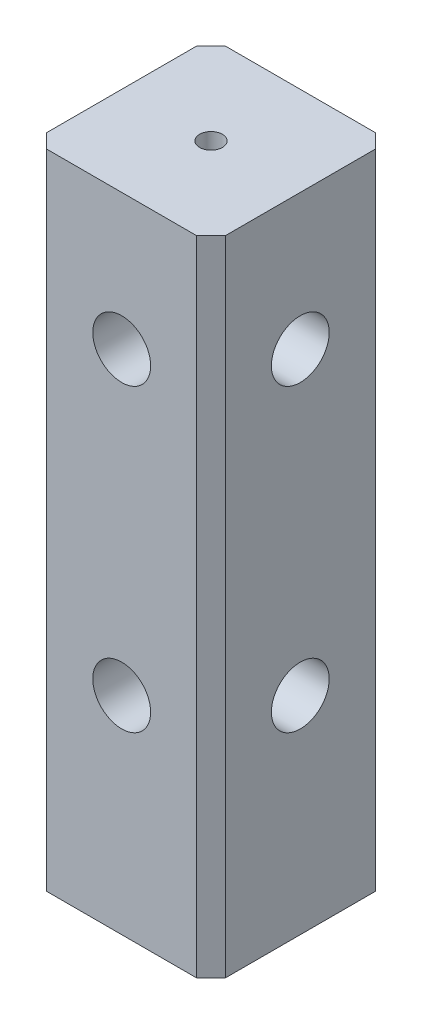
SolidWorks part; units mm, degrees
ref_plane "Front Plane" through (0, 0, 0) normal (0, 0, 1) x (1, 0, 0)
ref_plane "Top Plane" through (0, 0, 0) normal (0, 1, 0) x (1, 0, 0)
ref_plane "Right Plane" through (0, 0, 0) normal (1, 0, 0) x (0, 0, -1)
sketch "Sketch1" plane through (0, 0, 0) normal (0, 1, 0) x (1, 0, 0)
  line L1 (12.5, 12.5) -> (-12.5, 12.5)
  line L2 (12.5, 12.5) -> (12.5, -12.5)
  line L3 (12.5, -12.5) -> (-12.5, -12.5)
  line L4 (-12.5, 12.5) -> (-12.5, -12.5)
  point P4 (0, 12.5)
  point P6 (12.5, 0)
  dimension "D1" = 25
  dimension "D2" = 25
extrude "Boss-Extrude1" add sketch "Sketch1" along normal blind 90
sketch "Sketch2" plane through (12.5, 0, 0) normal (1, 0, 0) x (0, 0, -1)
  line L0 (-12.5, 90) -> (12.5, 90) construction
  line L3 (12.5, 90) -> (12.5, 0) construction
  circle A0 centre (0, 71) radius 4.05
  circle A1 centre (0, 29) radius 4.05
  dimension "D1" = 12.5
  dimension "D3" = 42
  dimension "D4" = 19
  dimension "D5" = 12.5
extrude "Cut-Extrude1" cut sketch "Sketch2" against normal blind 8 contours A1 | A0
sketch "Sketch3" plane through (0, 0, 12.5) normal (0, 0, 1) x (1, 0, 0)
  line L0 (-12.5, 90) -> (12.5, 90) construction
  line L2 (12.5, 90) -> (12.5, 0) construction
  circle A0 centre (0, 29) radius 4.05
  circle A1 centre (0, 71) radius 4.05
  dimension "D1" = 19
  dimension "D2" = 42
  dimension "D3" = 12.5
  dimension "D4" = 12.5
extrude "Cut-Extrude7" cut sketch "Sketch3" against normal blind 8 contours A0 | A1
chamfer "Chamfer1" distance 2 angle 45 1 edges at (12.5, 45, 12.5)
sketch "Sketch4" plane through (0, 90, 0) normal (0, 1, 0) x (1, 0, 0)
sketch "Sketch5" plane through (0, 90, 0) normal (0, 1, 0) x (1, 0, 0)
  circle A0 centre (0, 0) radius 1.6
extrude "Cut-Extrude8" cut sketch "Sketch5" against normal blind 10
